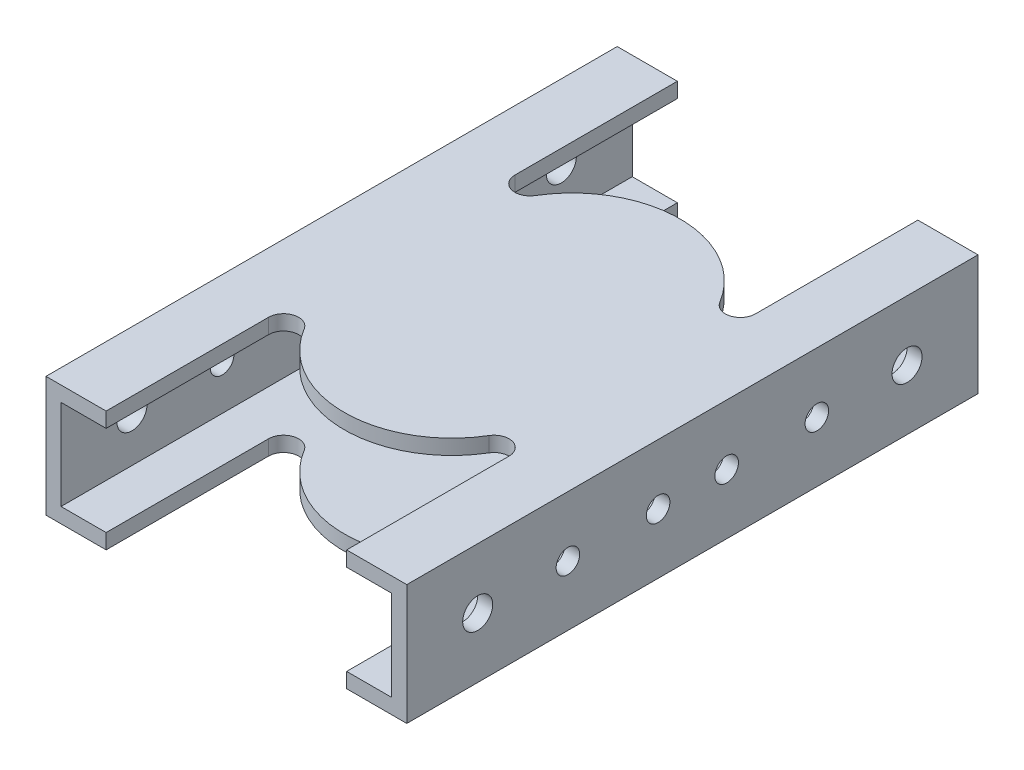
SolidWorks part; units mm, degrees
ref_plane "Front" through (0, 0, 0) normal (0, 0, 1) x (1, 0, 0)
ref_plane "Top" through (0, 0, 0) normal (0, 1, 0) x (1, 0, 0)
ref_plane "Right" through (0, 0, 0) normal (1, 0, 0) x (0, 0, -1)
sketch "Sketch1" plane through (0, 0, 0) normal (0, 0, 1) x (1, 0, 0)
  line L1 (-38.1, -12.7) -> (38.1, -12.7)
  line L2 (-38.1, -12.7) -> (-38.1, 12.7)
  line L3 (-38.1, 12.7) -> (38.1, 12.7)
  line L4 (38.1, -12.7) -> (38.1, 12.7)
  line L5 (-38.1, -12.7) -> (38.1, 12.7) construction
  line L6 (-38.1, 12.7) -> (38.1, -12.7) construction
  point P0 (0, 0)
  dimension "D1" = 25.4
  dimension "D2" = 76.2
extrude "Extrude-Thin1" add sketch "Sketch1" along normal blind 146.05 thin thin type one direction reverse wall 3.175
sketch "Sketch6" plane through (0, 12.7, 0) normal (0, 1, 0) x (1, 0, 0)
  line L1 (-38.1, -73.025) -> (38.1, -73.025) construction
  line L3 (-38.1, -146.05) -> (-38.1, 0) construction
  line L4 (-38.1, -12.7) -> (-25.4, -12.7)
  line L8 (-25.4, -12.7) -> (-25.4, -60.325)
  line L12 (25.4, -60.325) -> (25.4, -12.7)
  line L13 (-38.1, 0) -> (38.1, 0)
  line L14 (-38.1, 0) -> (-38.1, -12.7)
  line L15 (25.4, -12.7) -> (38.1, -12.7)
  line L18 (38.1, 0) -> (38.1, -12.7)
  line L19 (38.1, -146.05) -> (38.1, 0) construction
  arc A0 (19.5017, -48.6364) -> (25.4, -47.0042) centre (22.225, -47.0042) ccw
  arc A1 (-25.4, -47.0042) -> (-19.5017, -48.6364) centre (-22.225, -47.0042) ccw
  circle A4 centre (0, -60.325) radius 22.7363
  point P5 (-25.4, -38.7113)
  point P12 (0, 0)
  dimension "D5" = 12.7
  dimension "D3" = 45.4726
  dimension "D2" = 60.325
  dimension "D4" = 3.175
  dimension "D1" = 50.8
extrude "Cut-Extrude7" cut sketch "Sketch6" against normal through all
sketch "Sketch7" plane through (38.1, 0, 0) normal (1, 0, 0) x (0, 0, -1)
  line L0 (0, 0) -> (-27.686, 0) construction
  circle A0 centre (-27.686, 0) radius 3.175
  dimension "D1" = 6.35
  dimension "D2" = 27.686
extrude "Cut-Extrude8" cut sketch "Sketch7" against normal through all
ref_plane "Plane2" through (0, 0, 73.025) normal (0, 0, 1) x (1, 0, 0)
mirror "Mirror3" about plane through (0, 0, 73.025) normal (0, 0, 1) of "Cut-Extrude8", "Cut-Extrude7"
sketch "Sketch8" plane through (-38.1, 0, 0) normal (-1, 0, 0) x (0, 0, 1)
  line L0 (27.686, 0) -> (118.364, 0) construction
  circle A1 centre (46.736, 0) radius 2.4892
  circle A2 centre (99.314, 0) radius 2.4892
  circle A3 centre (80.264, 0) radius 2.4892
  circle A4 centre (65.786, 0) radius 2.4892
  dimension "D1" = 4.9784
  dimension "D2" = 19.05
  dimension "D3" = 19.05
  dimension "D4" = 19.05
  dimension "D5" = 19.05
extrude "Cut-Extrude9" cut sketch "Sketch8" against normal through all
equation "\"D3@Sketch8\"=\"D2@Sketch8\""
equation "\"D5@Sketch8\"=\"D2@Sketch8\""
equation "\"D4@Sketch8\"=\"D2@Sketch8\""
